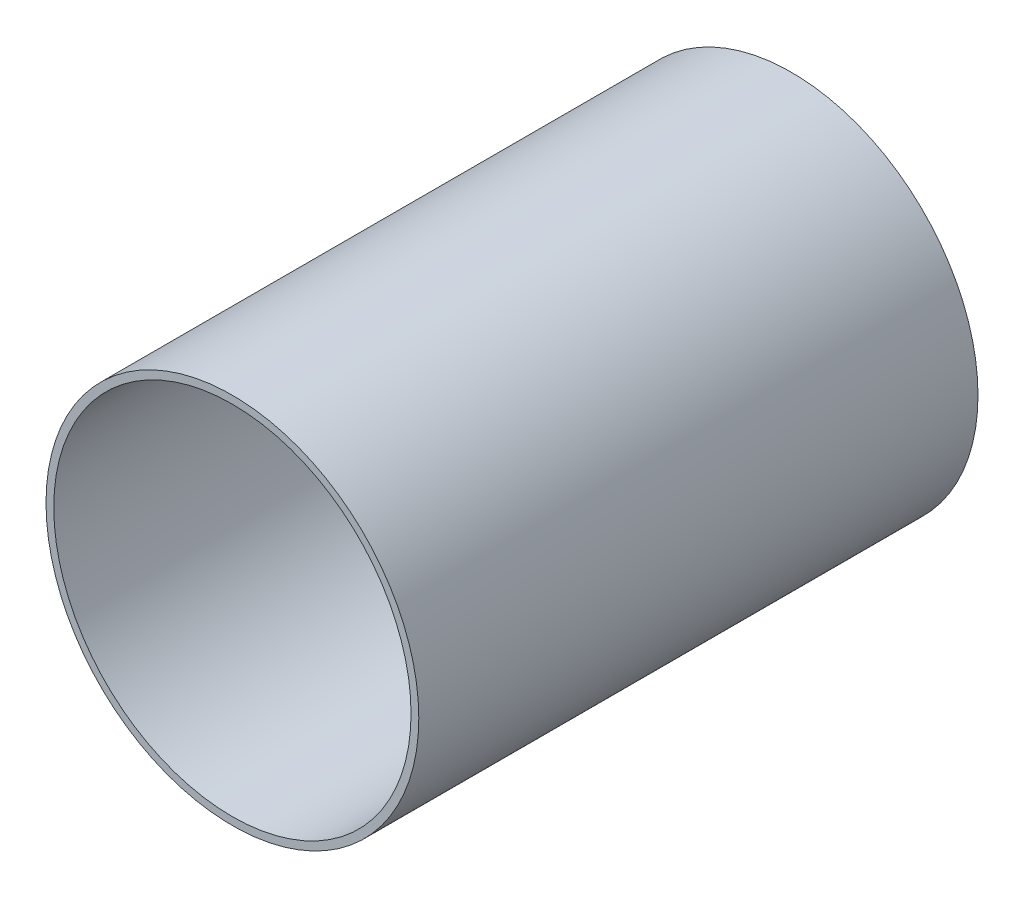
SolidWorks part; units mm, degrees
material "S-Glass Fiber"
ref_plane "Front Plane" through (0, 0, 0) normal (0, 0, 1) x (1, 0, 0)
ref_plane "Top Plane" through (0, 0, 0) normal (0, 1, 0) x (1, 0, 0)
ref_plane "Right Plane" through (0, 0, 0) normal (1, 0, 0) x (0, 0, -1)
sketch "Sketch1" plane through (0, 0, 0) normal (0, 0, 1) x (1, 0, 0)
  circle A0 centre (0, 0) radius 76.2
  circle A1 centre (0, 0) radius 73.025
  dimension "D1" = 152.4
  dimension "D2" = 3.175
extrude "Boss-Extrude1" add sketch "Sketch1" along normal blind 228.6
